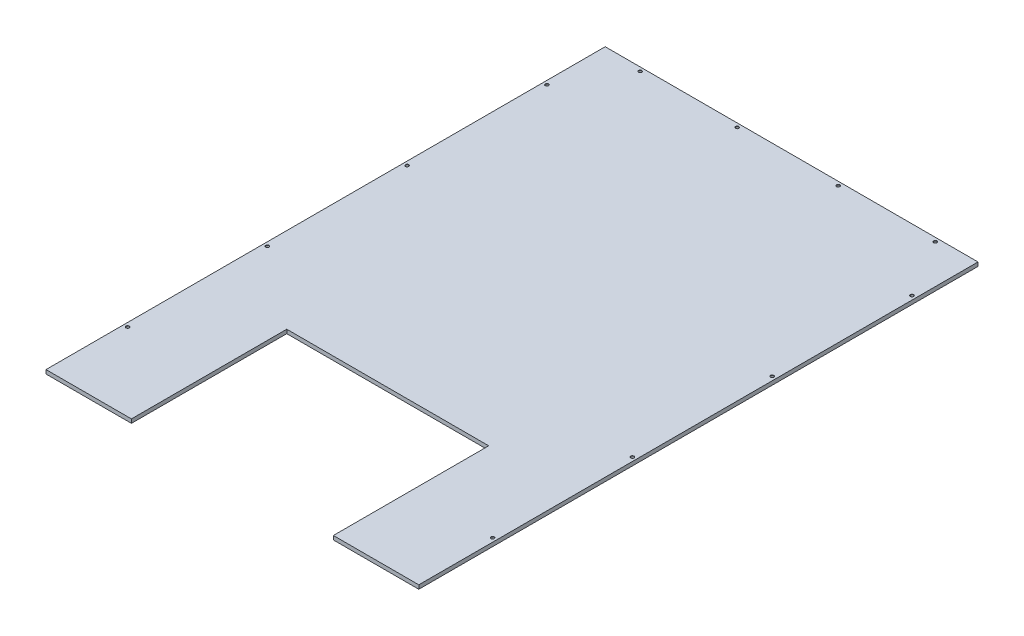
SolidWorks part; units mm, degrees
ref_plane "Front Plane" through (0, 0, 0) normal (0, 0, 1) x (1, 0, 0)
ref_plane "Top Plane" through (0, 0, 0) normal (0, 1, 0) x (1, 0, 0)
ref_plane "Right Plane" through (0, 0, 0) normal (1, 0, 0) x (0, 0, -1)
sketch "Sketch1" plane through (0, 0, 0) normal (0, 0, 1) x (1, 0, 0)
  line L1 (0, 0) -> (1219.2, 0)
  line L2 (0, 0) -> (0, 12.7)
  line L3 (0, 12.7) -> (1219.2, 12.7)
  line L4 (1219.2, 0) -> (1219.2, 12.7)
  dimension "D1" = 1219.2
  dimension "D2" = 12.7
extrude "Boss-Extrude1" add sketch "Sketch1" along normal blind 1828.8
sketch "Sketch2" plane through (0, 12.7, 0) normal (0, 1, 0) x (1, 0, 0)
  line L0 (279.4, -1828.8) -> (279.4, -1320.8)
  line L1 (1219.2, -1828.8) -> (0, -1828.8) construction
  line L2 (279.4, -1320.8) -> (939.8, -1320.8)
  line L3 (939.8, -1320.8) -> (939.8, -1828.8)
  line L4 (939.8, -1828.8) -> (279.4, -1828.8)
  line L7 (0, -1828.8) -> (0, 0) construction
  dimension "D1" = 508
  dimension "D2" = 660.4
  dimension "D3" = 279.4
extrude "Cut-Extrude1" cut sketch "Sketch2" against normal through all contours L2 L3 L4 L0
hole_wizard "3/8 (0.375) Diameter Hole1" positions "Sketch3" profile "Sketch4" hole size "3/8" standard "ANSI Inch" end condition through all
sketch "Sketch3" plane through (0, 12.7, 0) normal (0, 1, 0) x (1, 0, 0)
  line L0 (1219.2, -1828.8) -> (1219.2, 0) construction
  line L1 (0, -914.4) -> (1500.7176, -914.4) construction
  line L2 (0, -1828.8) -> (0, 0) construction
  line L4 (609.6, 0) -> (609.6, -2026.4593) construction
  line L5 (1219.2, 0) -> (0, 0) construction
  line L7 (1219.2, -1828.8) -> (939.8, -1828.8) construction
  point P0 (1206.5, -1574.8)
  point P2 (1206.5, -1117.6)
  point P4 (1206.5, -660.4)
  point P6 (1206.5, -203.2)
  point P25 (12.7, -1574.8)
  point P26 (12.7, -1117.6)
  point P27 (12.7, -660.4)
  point P28 (12.7, -203.2)
  point P29 (444.5, -12.7)
  point P31 (127, -12.7)
  point P35 (1092.2, -12.7)
  point P36 (774.7, -12.7)
  dimension "D1" = 12.7
  dimension "D2" = 254
  dimension "D3" = 457.2
  dimension "D4" = 457.2
  dimension "D5" = 457.2
  dimension "D6" = 12.7
  dimension "D7" = 127
  dimension "D8" = 165.1
sketch "Sketch4" plane through (1206.5, 12.7, 1574.8) normal (1, 0, 0) x (0, 0, 1)
  line L0 (0, 0) -> (0, 12.7)
  line L1 (0, 12.7) -> (4.7625, 12.7)
  line L2 (4.7625, 12.7) -> (4.7625, 0.635)
  line L3 (4.7625, 0.635) -> (5.3975, 0)
  line L5 (5.3975, 0) -> (0, 0)
  line L6 (-4.7625, 0.635) -> (-5.3975, 0) construction
  line L11 (0, -6.35) -> (0, 107.95) construction
  dimension "Thru Hole Dia." = 9.525
  dimension "Thru Hole Depth" = 12.7
  dimension "Near C'Sink Dia." = 10.795
  dimension "Near C'Sink Angle" = 90
